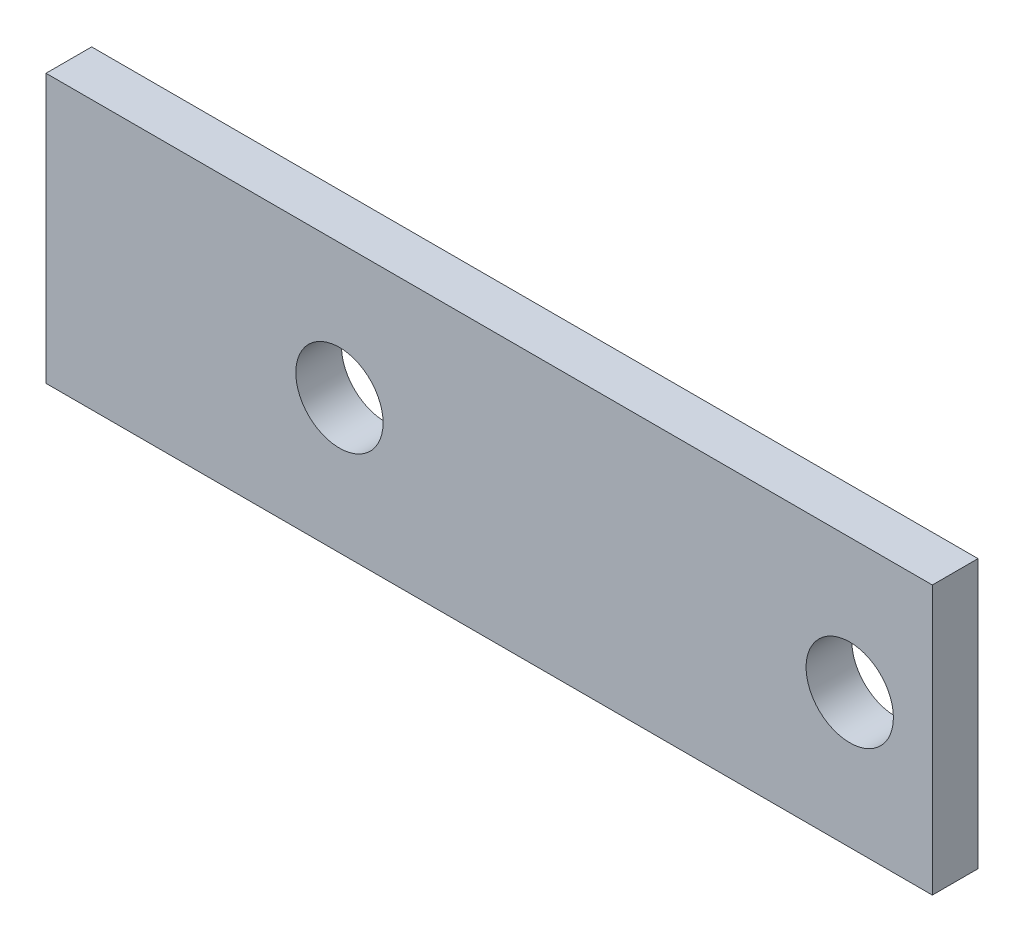
SolidWorks part; units mm, degrees
ref_plane "Plano frontal" through (0, 0, 0) normal (0, 0, 1) x (1, 0, 0)
ref_plane "Plano superior" through (0, 0, 0) normal (0, 1, 0) x (1, 0, 0)
ref_plane "Plano direito" through (0, 0, 0) normal (1, 0, 0) x (0, 0, -1)
sketch "Esboço1" plane through (0, 0, 0) normal (0, 0, 1) x (1, 0, 0)
  line L1 (-16.5, 5) -> (16.5, 5)
  line L2 (-16.5, 5) -> (-16.5, -5)
  line L3 (-16.5, -5) -> (16.5, -5)
  line L4 (16.5, 5) -> (16.5, -5)
  line L5 (-16.5, 5) -> (16.5, -5) construction
  line L6 (-16.5, -5) -> (16.5, 5) construction
  point P0 (0, 0)
  dimension "D1" = 33
  dimension "D2" = 10
extrude "Ressalto-extrusão1" add sketch "Esboço1" along normal blind 1.7
ref_plane "Plano1" through (0, 0, 0) normal (0, -1, 0) x (-1, 0, 0)
sketch "Esboço2" plane through (0, 0, 1.7) normal (0, 0, 1) x (1, 0, 0)
  circle A0 centre (-5.575, 0) radius 1.5 construction
  circle A1 centre (13.425, 0) radius 1.5 construction
  circle A2 centre (-5.575, 0) radius 1.5 construction
  circle A3 centre (13.425, 0) radius 1.5 construction
  circle A4 centre (13.425, 0) radius 1.625
  circle A5 centre (-5.575, 0) radius 1.625
  dimension "D2" = 0.125
extrude "Corte-extrusão1" cut sketch "Esboço2" against normal up to surface (1.7 mm away) up to face at (0, 0, 0)
